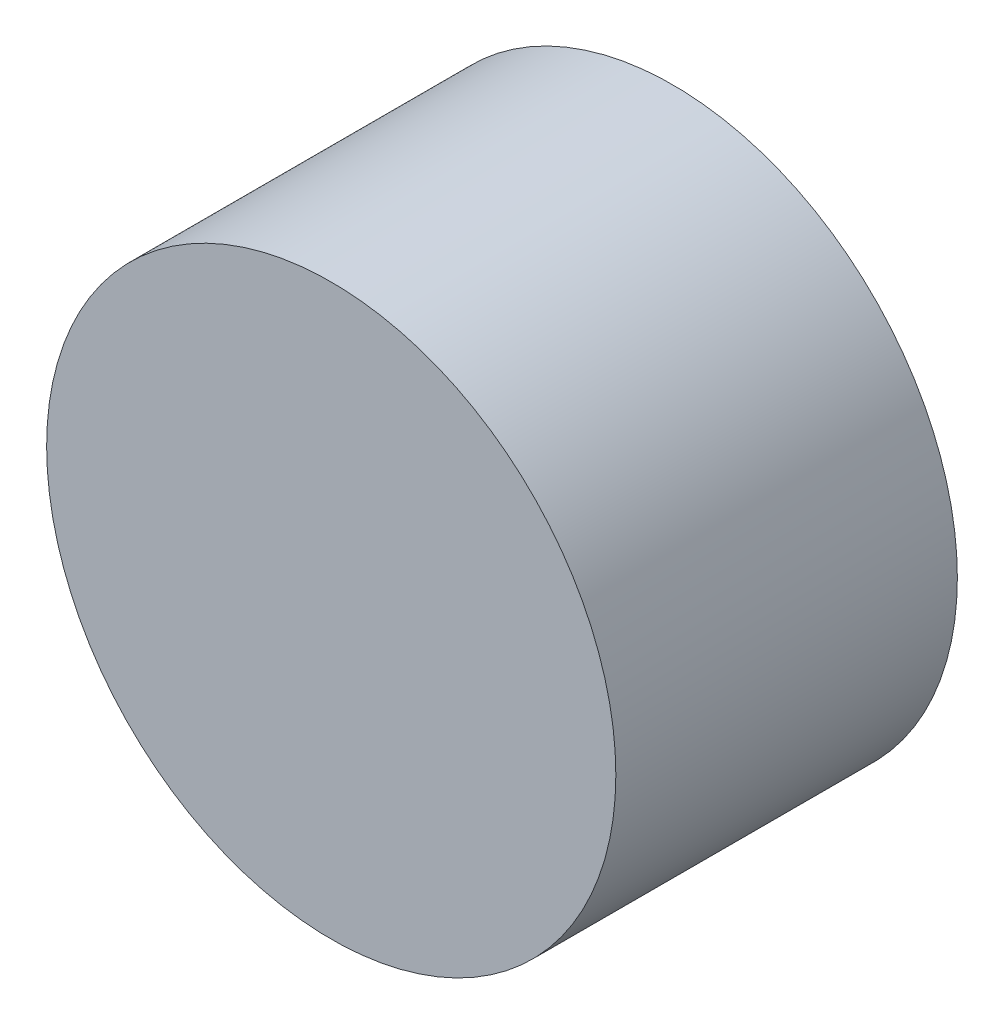
SolidWorks part; units mm, degrees
ref_plane "Piano frontale" through (0, 0, 0) normal (0, 0, 1) x (1, 0, 0)
ref_plane "Piano superiore" through (0, 0, 0) normal (0, 1, 0) x (1, 0, 0)
ref_plane "Piano destro" through (0, 0, 0) normal (1, 0, 0) x (0, 0, -1)
sketch "Schizzo1" plane through (0, 0, 0) normal (0, 0, 1) x (1, 0, 0)
  circle A0 centre (0, 0) radius 25
  dimension "D1" = 50
extrude "Estrusione-Estrusione1" add sketch "Schizzo1" along normal blind 30
